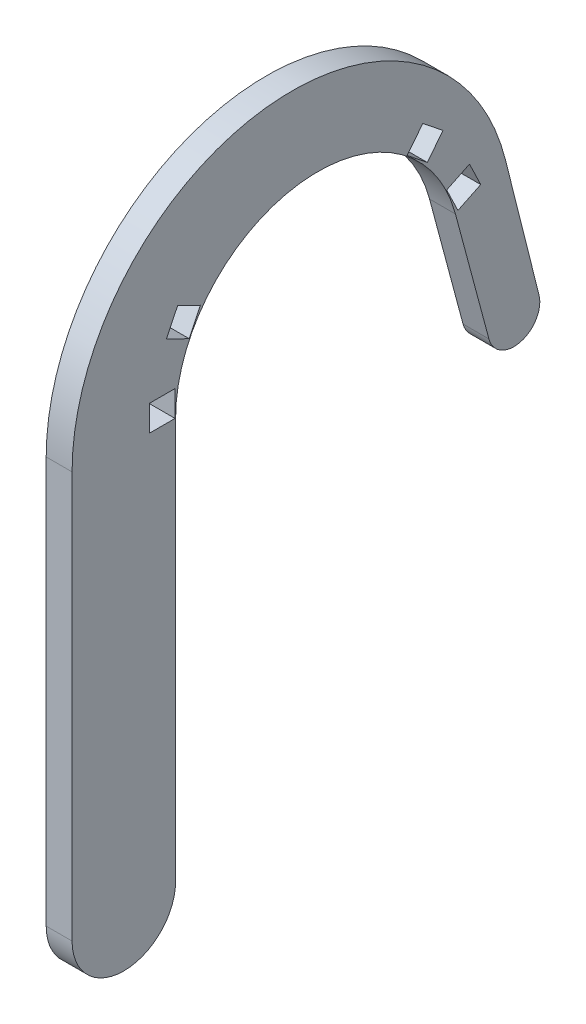
SolidWorks part; units mm, degrees
material "1060 Alloy"
ref_plane "Front Plane" through (0, 0, 0) normal (0, 0, 1) x (1, 0, 0)
ref_plane "Top Plane" through (0, 0, 0) normal (0, 1, 0) x (1, 0, 0)
ref_plane "Right Plane" through (0, 0, 0) normal (1, 0, 0) x (0, 0, -1)
sketch "Sketch1" plane through (0, 0, 0) normal (1, 0, 0) x (0, 0, -1)
  line L0 (-60.325, -98.425) -> (-60.325, 1.27)
  line L2 (-34.925, 0) -> (-34.925, -98.425)
  line L8 (46.0016, 14.4082) -> (54.2451, -18.4397)
  line L10 (41.9525, -21.6289) -> (33.735, 9.0393)
  arc A0 (46.0016, 14.4082) -> (-60.325, 1.27) centre (-6.35, 1.27) ccw
  arc A2 (33.735, 9.0393) -> (-34.925, 0) centre (0, 0) ccw
  arc A4 (41.9525, -21.6289) -> (54.2451, -18.4397) centre (48.0861, -19.9854) ccw
  arc A5 (-34.925, -98.425) -> (-60.325, -98.425) centre (-47.625, -98.425) cw
  dimension "D1" = 34.925
  dimension "D8" = 1.27
  dimension "D11" = 6.35
  dimension "D3" = 98.425
  dimension "D2" = 25.4
  dimension "D4" = 15
  dimension "D7" = 6.35
  dimension "D9" = 31.75
extrude "Boss-Extrude1" add sketch "Sketch1" along normal blind 6.35
sketch "Sketch5" plane through (6.35, 0, 0) normal (1, 0, 0) x (0, 0, -1)
  line L3 (-38.1, 6.35) -> (-41.275, 6.35)
  line L4 (-41.275, 0) -> (-41.275, 6.35)
  line L5 (-38.1, 6.35) -> (-35.0617, 6.35)
  line L6 (-35.0617, 6.35) -> (-35.0617, 0)
  line L8 (-35.0617, 0) -> (-41.275, 0)
sketch "Sketch6" plane through (0, 0, 0) normal (1, 0, 0) x (0, 0, -1)
  line L1 (-25.4, -44.014) -> (25.4, -44.014) construction
  line L2 (-25.4, -44.014) -> (-25.4, 6.786) construction
  line L3 (-25.4, 6.786) -> (25.4, 6.786) construction
  line L4 (25.4, -44.014) -> (25.4, 6.786) construction
  line L5 (-25.4, -44.014) -> (25.4, 6.786) construction
  line L6 (-25.4, 6.786) -> (25.4, -44.014) construction
  point P0 (0, -18.614)
  dimension "D1" = 50.8
  dimension "D2" = 50.8
extrude "Cut-Extrude2" cut sketch "Sketch5" against normal through all both and the other way through all
pattern_circular "CirPattern2" count 8 over 180 about axis through (0, 0, 0) along (1, 0, 0) skipping 2, 3, 4, 7 of "Cut-Extrude2"
